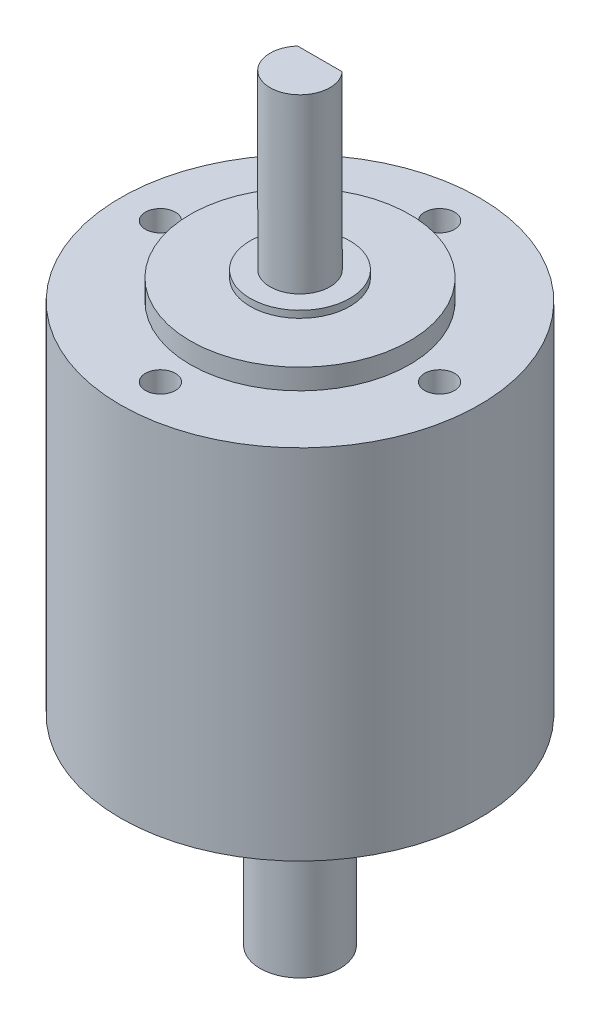
SolidWorks part; units mm, degrees
ref_plane "Front Plane" through (0, 0, 0) normal (0, 0, 1) x (1, 0, 0)
ref_plane "Top Plane" through (0, 0, 0) normal (0, 1, 0) x (1, 0, 0)
ref_plane "Right Plane" through (0, 0, 0) normal (1, 0, 0) x (0, 0, -1)
sketch "Sketch1" plane through (0, 0, 0) normal (0, 1, 0) x (1, 0, 0)
  circle A0 centre (0, 0) radius 18
  dimension "D1" = 36
extrude "Boss-Extrude1" add sketch "Sketch1" along normal mid plane 35.8902
sketch "Sketch2" plane through (0, 17.9451, 0) normal (0, 1, 0) x (1, 0, 0)
  circle A0 centre (0, 0) radius 11
  dimension "D1" = 22
extrude "Boss-Extrude2" add sketch "Sketch2" along normal mid plane 40.005 from surface at -17.9451 starting at plane "Top Plane"
sketch "Sketch3" plane through (0, 20.0025, 0) normal (0, 1, 0) x (1, 0, 0)
  circle A0 centre (0, 0) radius 3
  dimension "D1" = 6
extrude "Boss-Extrude4" add sketch "Sketch3" along normal blind 18
sketch "Sketch4" plane through (0, 38.0025, 0) normal (0, 1, 0) x (1, 0, 0)
  line L0 (-2.2361, 2) -> (2.2361, 2)
  line L1 (0, -3) -> (0, 2) construction
  arc A0 (0, -3) -> (2.2361, 2) centre (0, 0) ccw construction
  circle A1 centre (0, 0) radius 3
  arc A2 (2.2361, 2) -> (-2.2361, 2) centre (0, 0) ccw
  arc A3 (-2.2361, 2) -> (0, -3) centre (0, 0) ccw construction
  dimension "D2" = 5
  dimension "D1" = 0
extrude "Cut-Extrude1" cut sketch "Sketch4" against normal blind 15
sketch "Sketch5" plane through (0, 17.9451, 0) normal (0, 1, 0) x (1, 0, 0)
  circle A0 centre (0, 0) radius 14 construction
  circle A1 centre (0, 14) radius 1.5
  circle A2 centre (-14, 0) radius 1.5
  circle A3 centre (0, -14) radius 1.5
  circle A4 centre (14, 0) radius 1.5
  dimension "D1" = 28
  dimension "D2" = 3
extrude "Cut-Extrude2" cut sketch "Sketch5" against normal blind 4
mirror "Mirror1" about plane through (0, 0, 0) normal (0, 1, 0) of "Cut-Extrude2", "Cut-Extrude1"
sketch "Sketch6" plane through (0, -20.0025, 0) normal (0, -1, 0) x (1, 0, 0)
  circle A0 centre (0, 0) radius 4
  dimension "D1" = 8
extrude "Boss-Extrude5" add sketch "Sketch6" along normal blind 18
sketch "Sketch7" plane through (0, -38.0025, 0) normal (0, -1, 0) x (1, 0, 0)
  line L0 (-2.6458, -3) -> (2.6458, -3)
  line L1 (0, -3) -> (0, -4) construction
  arc A0 (2.6458, -3) -> (-2.6458, -3) centre (0, 0) cw
  circle A2 centre (0, 0) radius 4 construction
  dimension "D1" = 1
extrude "Cut-Extrude3" cut sketch "Sketch7" against normal offset from surface (15 mm away) 3 up to face at (0, -20.0025, -4)
sketch "Sketch9" plane through (0, 0, 0) normal (0, 1, 0) x (1, 0, 0)
  circle A0 centre (0, 0) radius 5
  dimension "D1" = 10
extrude "Boss-Extrude6" add sketch "Sketch9" along normal mid plane 41.402
